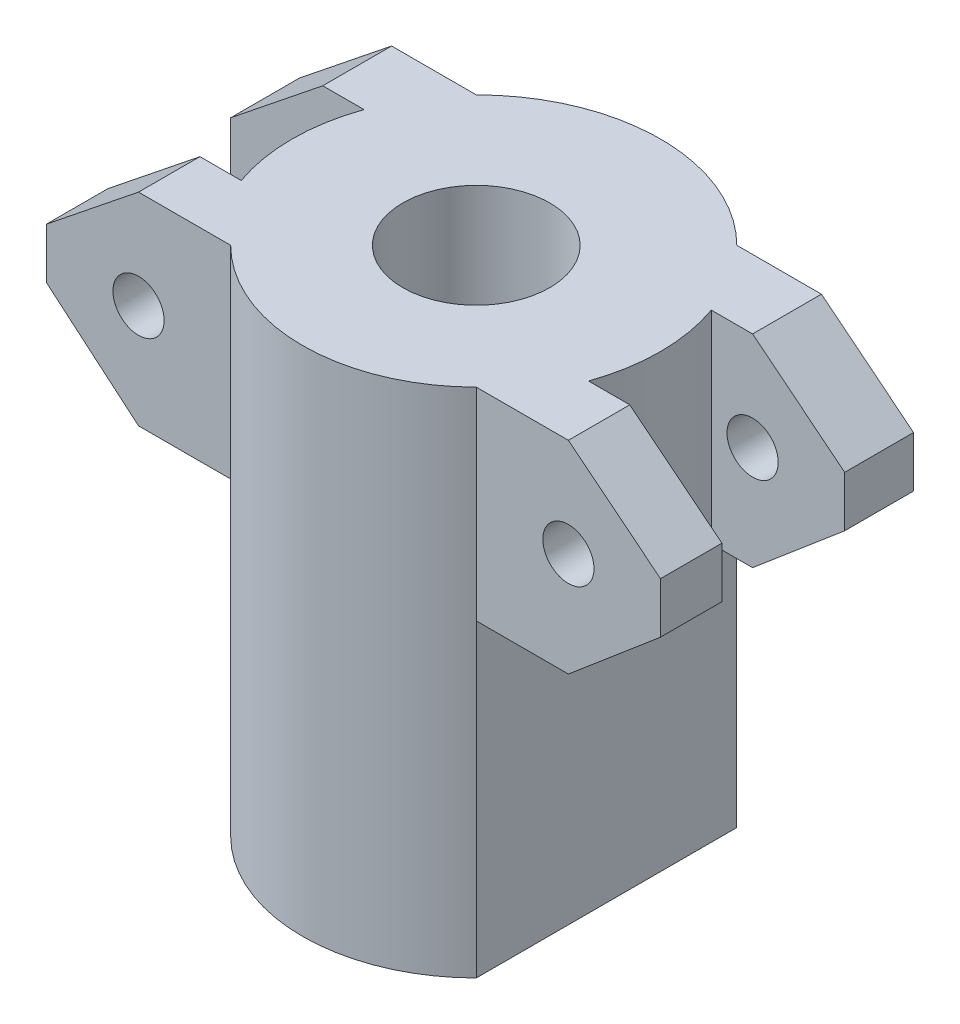
SolidWorks part; units mm, degrees
ref_plane "Спереди" through (0, 0, 0) normal (0, 0, 1) x (1, 0, 0)
ref_plane "Сверху" through (0, 0, 0) normal (0, 1, 0) x (1, 0, 0)
ref_plane "Справа" through (0, 0, 0) normal (1, 0, 0) x (0, 0, -1)
sketch "Эскиз1" plane through (0, 0, 0) normal (0, 1, 0) x (1, 0, 0)
  line L0 (-30, 12.7279) -> (-30, 6)
  line L1 (-30, -12) -> (-12, -12)
  line L2 (-30, 12.7279) -> (-12.7279, 12.7279)
  line L3 (0, 32.5643) -> (0, -33.2451) construction
  line L4 (30, 12.7279) -> (12.7279, 12.7279)
  line L5 (30, 12.7279) -> (30, 6)
  line L6 (30, 6) -> (16.9638, 6)
  line L7 (-30, 6) -> (-16.9638, 6)
  line L8 (30, -12) -> (12, -12)
  line L9 (-16.9638, -6) -> (-30, -6)
  line L10 (-30, -6) -> (-30, -12)
  line L11 (30, -6) -> (30, -12)
  line L12 (16.9638, -6) -> (30, -6)
  arc A0 (-12.7279, 12.7279) -> (12.7279, 12.7279) centre (0, 0) cw
  arc A1 (-12, -12) -> (12, -12) centre (0, 0) ccw
  circle A2 centre (0, 0) radius 7.1798
  arc A3 (-16.9638, 6) -> (-16.9638, -6) centre (0, 0) ccw
  arc A4 (16.9638, 6) -> (16.9638, -6) centre (0, 0) cw
  point P2 (-15.6393, 5.6999)
  point P6 (-16.9257, -6.1255)
  point P14 (0, 0)
  point P16 (0, 0)
  point P17 (-16.9706, 6)
  point P19 (0, 0)
  point P20 (0, 0)
  point P21 (0, 0)
  point P24 (0, 0)
  point P25 (0, 0)
  point P26 (0, 0)
  point P27 (0, 0)
  point P28 (0, 0)
extrude "Бобышка-Вытянуть1" add sketch "Эскиз1" along normal blind 50
sketch "Эскиз3" plane through (0, 0, 0) normal (0, 0, 1) x (1, 0, 0)
  line L5 (21, 50) -> (-21, 50)
  line L7 (12, 50) -> (-12, 50) construction
  line L8 (-30, 50) -> (-12, 50) construction
  line L11 (-21, 50) -> (-30, 42.792)
  line L12 (-30, 50) -> (-30, 0) construction
  line L13 (-30, 42.792) -> (-30, 37.8417)
  line L14 (-30, 37.8417) -> (-21, 30.2209)
  line L15 (-21, 30.2209) -> (-12, 30.2209)
  line L16 (-12, 50) -> (-12, 0) construction
  line L17 (-12, 30.2209) -> (-12, 0)
  line L18 (-12, 0) -> (12, 0)
  line L19 (-12, 0) -> (12, 0) construction
  line L20 (0, 54.386) -> (0, -5.9941) construction
  line L21 (12, 30.2209) -> (12, 0)
  line L22 (21, 30.2209) -> (12, 30.2209)
  line L23 (30, 37.8417) -> (21, 30.2209)
  line L24 (30, 42.792) -> (30, 37.8417)
  line L25 (21, 50) -> (30, 42.792)
  circle A0 centre (-21, 40.382) radius 2.5
  circle A1 centre (21, 40.382) radius 2.5
  point P22 (0, 0)
  point P28 (0, 0)
  point P35 (0, 50)
extrude "Вырез-Вытянуть1" cut sketch "Эскиз3" against normal through all both and the other way through all flip side to cut
